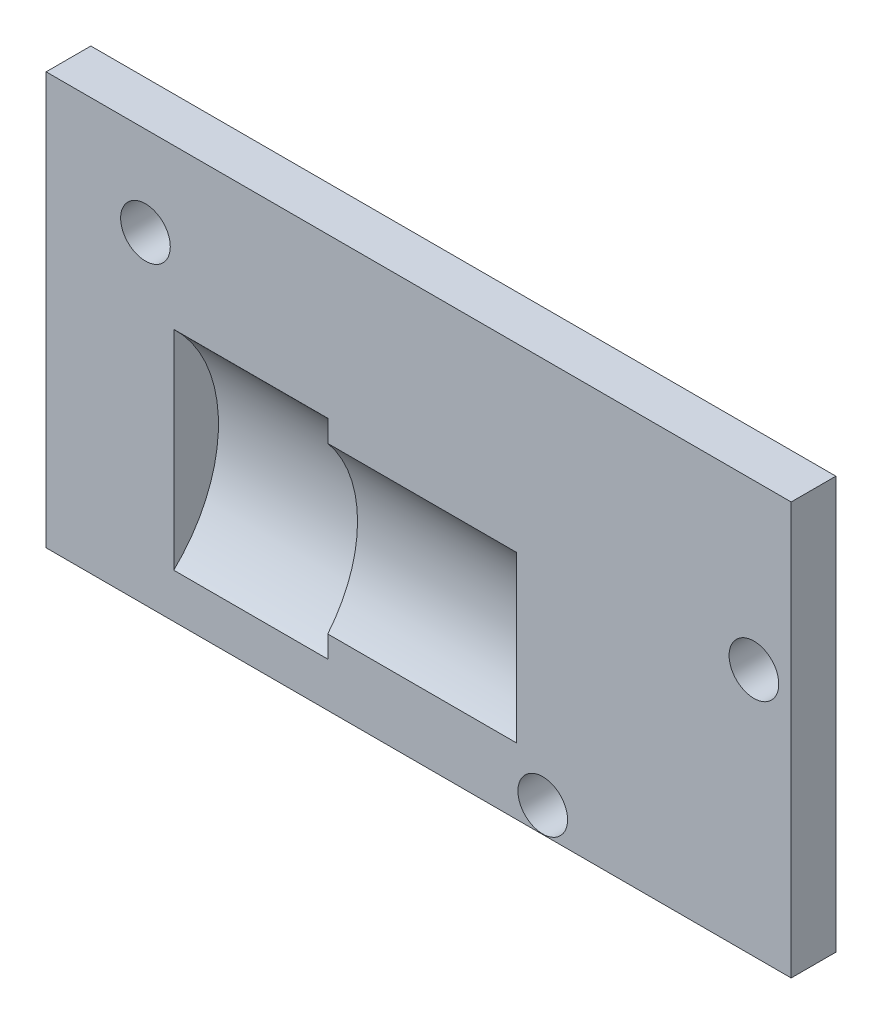
SolidWorks part; units mm, degrees
ref_plane "Front Plane" through (0, 0, 0) normal (0, 0, 1) x (1, 0, 0)
ref_plane "Top Plane" through (0, 0, 0) normal (0, 1, 0) x (1, 0, 0)
ref_plane "Right Plane" through (0, 0, 0) normal (1, 0, 0) x (0, 0, -1)
sketch "Sketch1" plane through (0, 0, 0) normal (0, 0, 1) x (1, 0, 0)
  line L0 (7.5, -4.15) -> (-7.5, -4.15)
  line L1 (7.5, 4.15) -> (-7.5, 4.15)
  line L2 (7.5, 4.15) -> (7.5, -4.15)
  line L4 (-7.5, 4.15) -> (-7.5, -4.15)
  line L5 (7.5, 4.15) -> (-7.5, -4.15) construction
  line L6 (7.5, -4.15) -> (-7.5, 4.15) construction
  circle A0 centre (-5.5, 2.35) radius 0.5
  circle A1 centre (6.75, 0.85) radius 0.5
  circle A2 centre (2.4984, -3.64) radius 0.5
  point P0 (0, 0)
  dimension "D3" = 1
  dimension "D4" = 1.8
  dimension "D5" = 2
  dimension "D6" = 0.75
  dimension "D7" = 1
  dimension "D1" = 5
  dimension "D2" = 8.3
  dimension "D8" = 5.0016
  dimension "D9" = 0.51
  dimension "D10" = 15
extrude "Front Face Ext" add sketch "Sketch1" along normal blind 0.9
ref_plane "Plane1" through (-5.93, 0, 0) normal (-1, 0, 0) x (0, 0, 1)
sketch "Sketch3" plane through (-5.93, 0, 0) normal (-1, 0, 0) x (0, 0, 1)
  line L0 (0, 0.65) -> (0, -2.96)
  line L1 (0.9, 4.15) -> (0, 4.15) construction
  line L4 (0, 4.15) -> (0, -4.15)
  line L5 (0, -4.15) -> (0.9, -4.15)
  line L6 (0.9, -4.15) -> (0.9, 4.15)
  line L7 (0.9, 4.15) -> (0, 4.15)
  line L8 (0, 4.15) -> (0, -4.15) construction
  line L9 (0, -4.15) -> (0.9, -4.15) construction
  line L10 (0.9, -4.15) -> (0.9, 4.15) construction
  line L11 (0.9, 4.15) -> (0, 4.15) construction
  arc A1 (0, -2.96) -> (0, 0.65) centre (2.9987, -1.155) cw
  point P9 (0, -1.155)
  dimension "D4" = 3.5
  dimension "D2" = 3.5
  dimension "D3" = 3.61
  dimension "D5" = 5.305
  dimension "D1" = 0
extrude "Boss-Extrude1" add sketch "Sketch3" against normal blind 8.4 from offset 0.3 offset against normal yes
sketch "Sketch4" plane through (-5.93, 0, 0) normal (-1, 0, 0) x (0, 0, 1)
  line L0 (0.9, -4.15) -> (0, -4.15) construction
  line L1 (0.9, 4.15) -> (0, 4.15) construction
  line L2 (0.9, 4.15) -> (0.9, -4.15) construction
  line L3 (0.9, -4.15) -> (0, -4.15) construction
  line L4 (0.9, 4.15) -> (0, 4.15) construction
  line L5 (0.9, 4.15) -> (0.9, -4.15) construction
  line L6 (0.9, -1.155) -> (2.9, -1.155) construction
  line L7 (2.9, -1.155) -> (2.0885, -1.155) construction
  line L8 (2.0885, -4.06) -> (2.0885, 1.75) construction
  line L9 (0.9, 0.945) -> (0.9, -3.255)
  arc A0 (0.9, 0.945) -> (0.9, -3.255) centre (2.9, -1.155) ccw
  point P10 (2.0885, -1.155)
  point P11 (0.9, 0.945)
  point P12 (0.9, -3.255)
  dimension "D4" = 2.9
  dimension "D1" = 2
  dimension "D2" = 5.305
  dimension "D3" = 2.4
extrude "Cut-Extrude5" cut sketch "Sketch4" against normal blind 3.1 from offset 1 contours L9 A0 offset against normal yes
sketch "Sketch6" plane through (-1.83, 0, 0) normal (-1, 0, 0) x (0, 0, 1)
  line L0 (0.9, 0.945) -> (0.9, -3.255) construction
  line L1 (0.9, 0.5063) -> (0.9, -2.8163)
  arc A2 (1.1069, 0.7278) -> (1.1069, -3.0378) centre (2.9, -1.155) ccw
  arc A3 (0.9, 0.5063) -> (0.9, -2.8163) centre (2.9, -1.155) ccw
  dimension "D1" = 0.3
extrude "Cut-Extrude6" cut sketch "Sketch6" against normal blind 3.8
